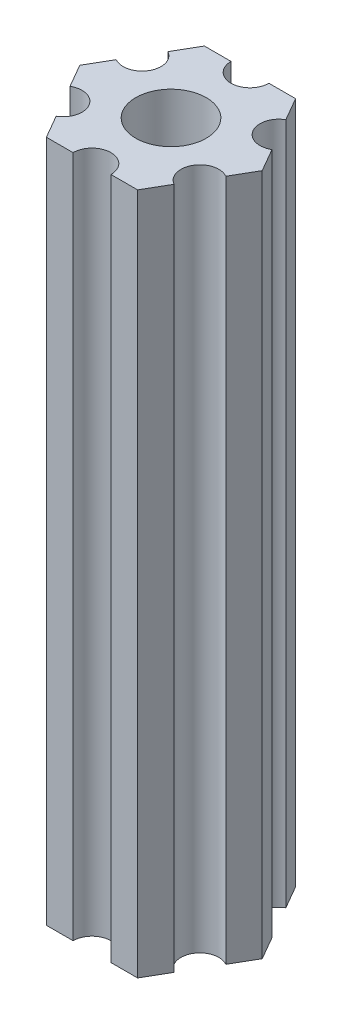
SolidWorks part; units mm, degrees
material "Churro - 6005A-T61"
ref_plane "Plano frontal" through (0, 0, 0) normal (0, 0, 1) x (1, 0, 0)
ref_plane "Plano superior" through (0, 0, 0) normal (0, 1, 0) x (1, 0, 0)
ref_plane "Plano direito" through (0, 0, 0) normal (1, 0, 0) x (0, 0, -1)
ref_plane "Plano1" through (0, 85, 0) normal (0, 1, 0) x (1, 0, 0)
sketch "Esboço1" plane through (0, 85, 0) normal (0, 1, 0) x (1, 0, 0)
  line L0 (6.1627, -1.826) -> (7.2169, 0)
  line L1 (7.2169, 0) -> (6.1627, 1.826)
  line L2 (4.6627, 4.424) -> (3.6084, 6.25)
  line L3 (3.6084, 6.25) -> (1.5, 6.25)
  line L4 (-1.5, 6.25) -> (-3.6084, 6.25)
  line L5 (-3.6084, 6.25) -> (-4.6627, 4.424)
  line L6 (-6.1627, 1.826) -> (-7.2169, 0)
  line L7 (-7.2169, 0) -> (-6.1627, -1.826)
  line L8 (-4.6627, -4.424) -> (-3.6084, -6.25)
  line L9 (-3.6084, -6.25) -> (-1.5, -6.25)
  line L10 (1.5, -6.25) -> (3.6084, -6.25)
  line L11 (3.6084, -6.25) -> (4.6627, -4.424)
  arc A0 (6.1627, 1.826) -> (4.6627, 4.424) centre (5.4127, 3.125) cw
  arc A1 (1.5, 6.25) -> (-1.5, 6.25) centre (0, 6.25) cw
  arc A2 (-4.6627, 4.424) -> (-6.1627, 1.826) centre (-5.4127, 3.125) cw
  arc A3 (-6.1627, -1.826) -> (-4.6627, -4.424) centre (-5.4127, -3.125) cw
  arc A4 (-1.5, -6.25) -> (1.5, -6.25) centre (0, -6.25) cw
  arc A5 (4.6627, -4.424) -> (6.1627, -1.826) centre (5.4127, -3.125) cw
  circle A6 centre (0, 0) radius 2.79
extrude "Ressalto-extrusão1" add sketch "Esboço1" against normal blind 54
